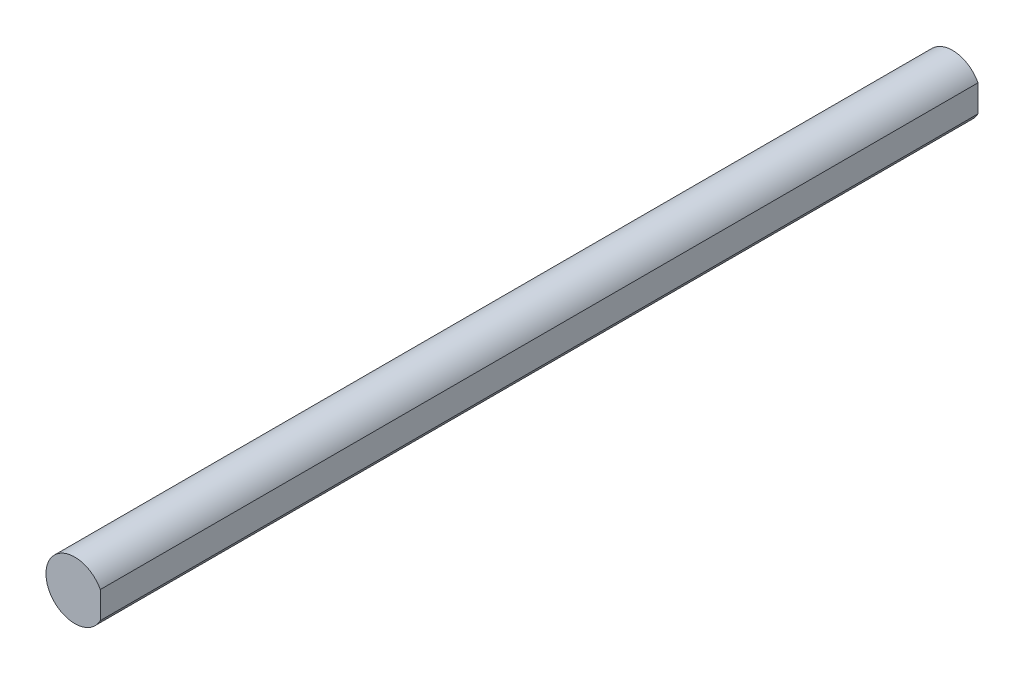
SolidWorks part; units mm, degrees
ref_plane "Front Plane" through (0, 0, 0) normal (0, 0, 1) x (1, 0, 0)
ref_plane "Top Plane" through (0, 0, 0) normal (0, 1, 0) x (1, 0, 0)
ref_plane "Right Plane" through (0, 0, 0) normal (1, 0, 0) x (0, 0, -1)
sketch "Sketch2" plane through (0, 0, 0) normal (0, 0, 1) x (1, 0, 0)
  line L0 (2.5843, -2.921) -> (2.5843, 3.7035)
  circle A0 centre (0, 0) radius 2.921
  dimension "D1" = 5.842
extrude "Boss-Extrude2" add sketch "Sketch2" along normal blind 88.9 contours L0 A0
